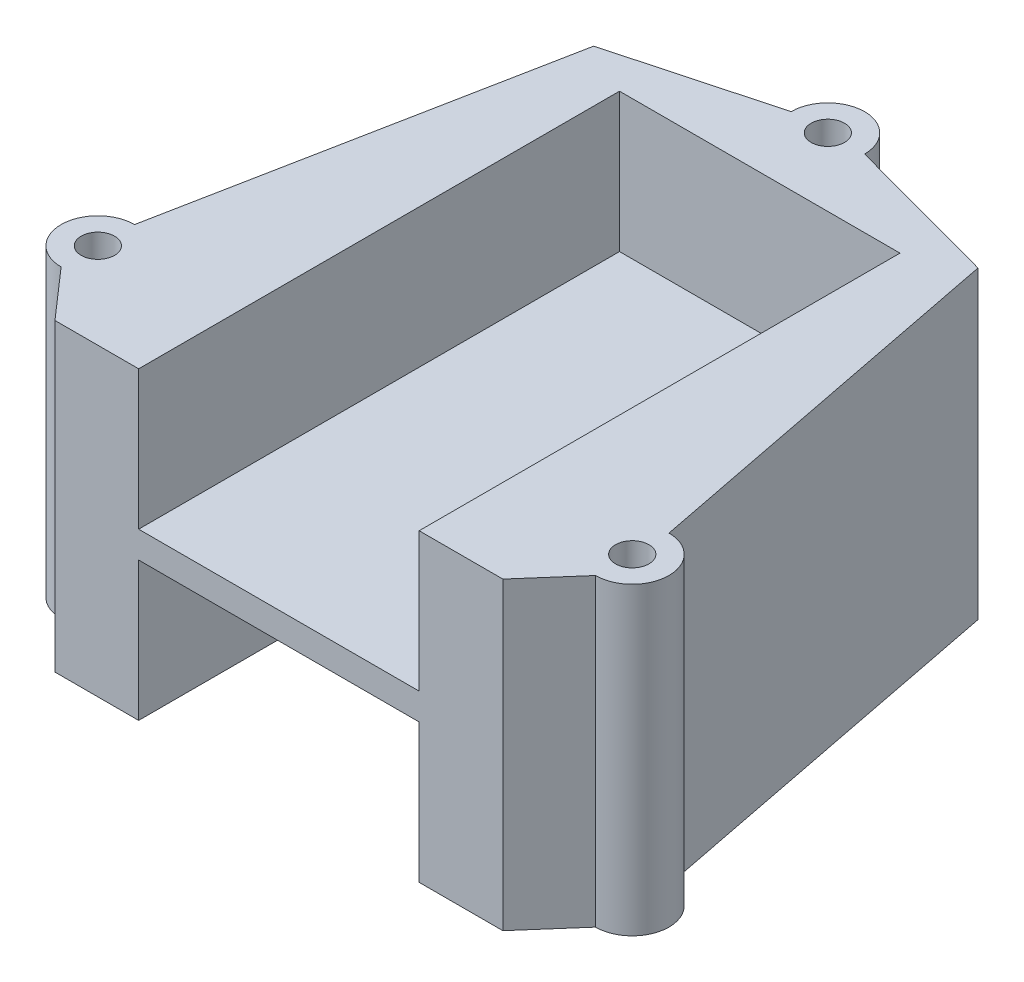
SolidWorks part; units mm, degrees
ref_plane "Front Plane" through (0, 0, 0) normal (0, 0, 1) x (1, 0, 0)
ref_plane "Top Plane" through (0, 0, 0) normal (0, 1, 0) x (1, 0, 0)
ref_plane "Right Plane" through (0, 0, 0) normal (1, 0, 0) x (0, 0, -1)
sketch "Sketch1" plane through (0, 0, 0) normal (0, 1, 0) x (1, 0, 0)
  line L0 (0, 0) -> (0, 38.1)
  circle A0 centre (0, 0) radius 38.1
  circle A2 centre (0, 29.337) radius 1.5875
  circle A3 centre (25.4066, -14.6685) radius 1.5875
  circle A4 centre (-25.4066, -14.6685) radius 1.5875
  point P12 (0, 0)
  dimension "D1" = 3.175
  dimension "D3" = 76.2
  dimension "D2" = 8.763
  dimension "D4" = 3
extrude "Boss-Extrude1" add sketch "Sketch1" along normal blind 2.54
sketch "Sketch2" plane through (0, 2.54, 0) normal (0, 1, 0) x (1, 0, 0)
  line L1 (13.335, 2.54) -> (0, 2.54) construction
  line L14 (13.335, -20.32) -> (-13.335, -20.32)
  line L15 (13.335, -20.32) -> (13.335, 25.4)
  line L16 (13.335, 25.4) -> (-13.335, 25.4)
  line L17 (-13.335, -20.32) -> (-13.335, 25.4)
  line L18 (0, 38.1) -> (0, -38.1) construction
  line L19 (0, 2.54) -> (-13.335, 2.54) construction
  line L20 (25.4066, -11.176) -> (18.2707, 25.3425)
  line L21 (25.4066, -18.161) -> (21.2951, -22.86)
  line L22 (18.2707, 25.3425) -> (3.4925, 29.337)
  line L23 (21.2951, -22.86) -> (-21.2951, -22.86)
  line L24 (-18.2707, 25.3425) -> (-3.4925, 29.337)
  line L25 (-25.4066, -11.176) -> (-18.2707, 25.3425)
  line L26 (-25.4066, -18.161) -> (-21.2951, -22.86)
  circle A20 centre (0, 0) radius 29.337 construction
  circle A22 centre (0, 0) radius 38.1 construction
  circle A51 centre (0, 0) radius 31.242 construction
  circle A52 centre (25.4066, -14.6685) radius 3.4925
  circle A53 centre (25.4066, -14.6685) radius 3.4925
  circle A55 centre (-25.4066, -14.6685) radius 3.4925
  circle A56 centre (0, 29.337) radius 3.4925
  circle A57 centre (0, 29.337) radius 3.4925
  point P20 (10.8816, 27.3397)
  point P25 (-10.8816, 27.3397)
  point P36 (0, -22.86)
  dimension "D5" = 1.905
  dimension "D7" = 2.54
  dimension "D8" = 116.182
  dimension "D1" = 26.67
  dimension "D2" = 45.72
  dimension "D3" = 25.4
  dimension "D4" = 1.905
  dimension "D6" = 1.905
extrude "Boss-Extrude2" add sketch "Sketch2" along normal blind 28.956 separate body
delete or keep bodies "Body-Delete/Keep 1" type delete bodies bodies 101
sketch "Sketch3" plane through (0, 0, 22.86) normal (0, 0, 1) x (1, 0, 0)
  line L0 (0, 31.496) -> (0, 2.54) construction
  line L1 (13.335, 36.068) -> (-13.335, 36.068)
  line L2 (13.335, 36.068) -> (13.335, 18.288)
  line L3 (13.335, 18.288) -> (-13.335, 18.288)
  line L4 (-13.335, 36.068) -> (-13.335, 18.288)
  line L5 (21.2951, 31.496) -> (-21.2951, 31.496) construction
  line L6 (21.2951, 2.54) -> (-21.2951, 2.54) construction
  line L7 (13.335, 36.068) -> (21.2951, 36.068) construction
  line L8 (21.2951, 31.496) -> (21.2951, 2.54) construction
  line L9 (21.2951, 17.018) -> (-18.387, 17.018) construction
  line L11 (-13.335, -2.032) -> (-13.335, 15.748)
  line L12 (-13.335, 36.068) -> (-21.2951, 36.068) construction
  line L13 (-21.2951, 31.496) -> (-21.2951, 2.54) construction
  line L14 (13.335, 15.748) -> (-13.335, 15.748)
  line L15 (13.335, -2.032) -> (13.335, 15.748)
  line L16 (13.335, -2.032) -> (-13.335, -2.032)
  dimension "D1" = 17.78
  dimension "D2" = 26.67
  dimension "D3" = 1.27
extrude "Cut-Extrude1" cut sketch "Sketch3" against normal blind 45.72
ref_plane "Fastner Plane" through (0, 0, 12.7) normal (0, 0, 1) x (1, 0, 0)
